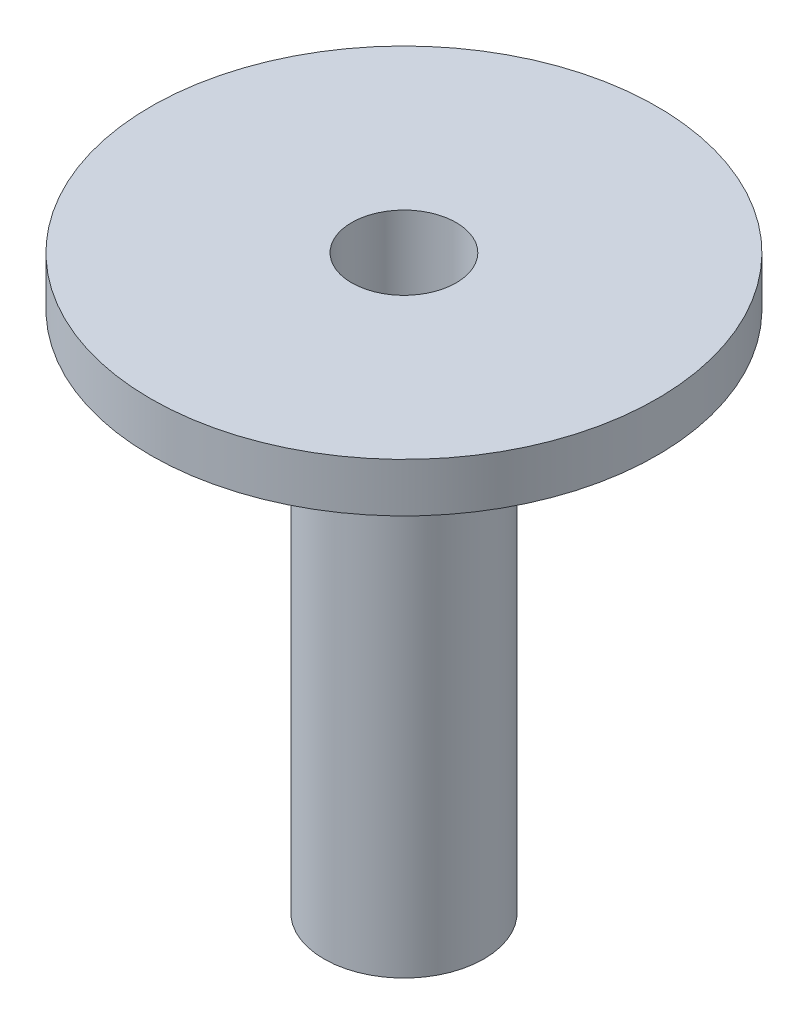
SolidWorks part; units mm, degrees
ref_plane "Front Plane" through (0, 0, 0) normal (0, 0, 1) x (1, 0, 0)
ref_plane "Top Plane" through (0, 0, 0) normal (0, 1, 0) x (1, 0, 0)
ref_plane "Right Plane" through (0, 0, 0) normal (1, 0, 0) x (0, 0, -1)
sketch "Sketch1" plane through (0, 0, 0) normal (0, 1, 0) x (1, 0, 0)
  circle A0 centre (0, 0) radius 6.75
  circle A1 centre (0, 0) radius 7.75
  dimension "D1" = 13.5
  dimension "D2" = 1
extrude "Boss-Extrude1" add sketch "Sketch1" along normal blind 1.5 contours A0 | A1 A0
sketch "Sketch2" plane through (0, 1.5, 0) normal (0, 1, 0) x (1, 0, 0)
  circle A0 centre (0, 0) radius 1.6
  dimension "D1" = 3.2
extrude "Cut-Extrude3" cut sketch "Sketch2" against normal through all
sketch "Sketch5" plane through (0, 0, 0) normal (0, -1, 0) x (-1, 0, 0)
  circle A0 centre (0, 0) radius 2.45
  circle A1 centre (0, 0) radius 1.6
  dimension "D1" = 4.9
  dimension "D2" = 3.2
extrude "Boss-Extrude3" add sketch "Sketch5" along normal blind 16
